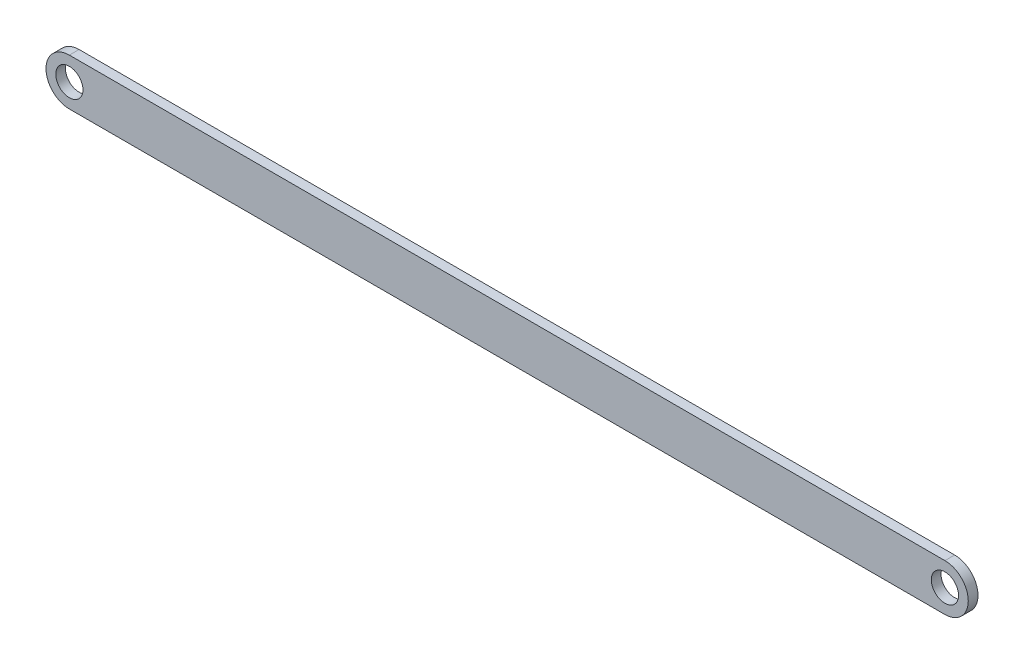
SolidWorks part; units mm, degrees
ref_plane "Płaszczyzna przednia" through (0, 0, 0) normal (0, 0, 1) x (1, 0, 0)
ref_plane "Płaszczyzna górna" through (0, 0, 0) normal (0, 1, 0) x (1, 0, 0)
ref_plane "Płaszczyzna prawa" through (0, 0, 0) normal (1, 0, 0) x (0, 0, -1)
sketch "Szkic1" plane through (0, 0, 0) normal (0, 0, 1) x (1, 0, 0)
  line L1 (0, 0) -> (450, 0)
  line L3 (0, 24) -> (450, 24)
  arc A0 (0, 24) -> (0, 0) centre (0, 12) ccw
  arc A1 (450, 0) -> (450, 24) centre (450, 12) ccw
  dimension "D1" = 24
  dimension "D2" = 450
extrude "Dodanie-wyciągnięcie1" add sketch "Szkic1" along normal blind 5
sketch "Szkic2" plane through (0, 0, 5) normal (0, 0, 1) x (1, 0, 0)
  circle A0 centre (0, 12) radius 7
  circle A1 centre (450, 12) radius 7
extrude "Wytnij-wyciągnięcie1" cut sketch "Szkic2" against normal blind 5
